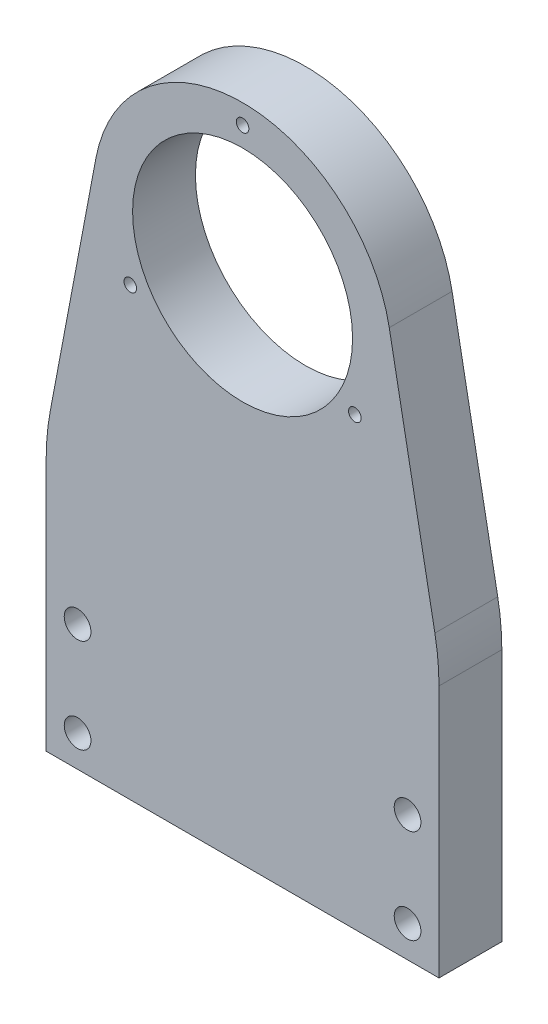
SolidWorks part; units mm, degrees
ref_plane "정면" through (0, 0, 0) normal (0, 0, 1) x (1, 0, 0)
ref_plane "윗면" through (0, 0, 0) normal (0, 1, 0) x (1, 0, 0)
ref_plane "우측면" through (0, 0, 0) normal (1, 0, 0) x (0, 0, -1)
sketch "스케치1" plane through (0, 0, 0) normal (0, 0, 1) x (1, 0, 0)
  line L0 (0, 0) -> (50, 0)
  line L1 (50, 0) -> (50, 35)
  line L2 (50, 35) -> (43.6701, 68.5251)
  line L3 (25, 0) -> (25, 65) construction
  line L4 (0, 35) -> (6.3299, 68.5251)
  line L5 (0, 0) -> (0, 35)
  circle A0 centre (25, 65) radius 19
  dimension "D1" = 38
  dimension "D3" = 65
  dimension "D4" = 50
  dimension "D5" = 35
extrude "보스-돌출1" add sketch "스케치1" along normal blind 8
fillet "필렛1" radius 30 2 edges at (0, 35, 4) (50, 35, 4)
sketch "스케치2" plane through (0, 0, 0) normal (0, 0, -1) x (-1, 0, 0)
  arc A0 (-6.3299, 68.5251) -> (-43.6701, 68.5251) centre (-25, 65) ccw construction
  arc A1 (-6.3299, 68.5251) -> (-43.6701, 68.5251) centre (-25, 65) ccw
  circle A2 centre (-25, 65) radius 14
  dimension "D1" = 28
extrude "컷-돌출1" cut sketch "스케치2" against normal up to next contours A2
hole_wizard "M3 육각 소켓 접시 머리 캡 나사용 카운터싱크1" positions "스케치3" profile "스케치4" countersink size "M3" standard "ISO" end condition up to next
sketch "스케치3" plane through (0, 0, 0) normal (0, 0, -1) x (-1, 0, 0)
  line L0 (-4, 16) -> (-4, 4)
  line L3 (0, 0) -> (0, 32.1927) construction
  line L4 (0, 0) -> (-50, 0) construction
  line L5 (-46, 16) -> (-46, 4)
  line L6 (-50, 0) -> (-50, 32.1927) construction
  point P0 (-4, 16)
  point P2 (-4, 4)
  point P20 (-46, 16)
  point P21 (-46, 4)
  point P30 (-46, 10)
  dimension "D1" = 12
  dimension "D2" = 4
  dimension "D3" = 4
  dimension "D4" = 4
sketch "스케치4" plane through (4, 16, 0) normal (1, 0, 0) x (0, 1, 0)
  line L0 (0, 0) -> (0, 8)
  line L1 (0, 8) -> (1.7, 8)
  line L2 (1.7, 8) -> (1.7, 1.66)
  line L3 (1.7, 1.66) -> (3.36, 0)
  line L5 (3.36, 0) -> (0, 0)
  line L6 (-1.7, 1.66) -> (-3.36, 0) construction
  line L11 (0, -6.35) -> (0, 107.95) construction
  dimension "관통 구멍 지름" = 3.4
  dimension "관통 구멍 깊이" = 8
  dimension "표면 카운터싱크 지름" = 6.72
  dimension "표면 카운터싱크 각도" = 90
hole_wizard "M3 나사 구멍1" positions "스케치5" profile "스케치6" tap size "M3" standard "ISO"
sketch "스케치5" plane through (0, 0, 0) normal (0, -1, 0) x (-1, 0, 0)
  line L0 (-38, -4) -> (-12, -4)
  line L2 (0, 0) -> (-50, 0) construction
  line L3 (0, -8) -> (0, 0) construction
  point P0 (-38, -4)
  point P2 (-12, -4)
  point P9 (-25, -4)
  point P12 (-25, 0)
  point P15 (0, -4)
  dimension "D1" = 12
sketch "스케치6" plane through (38, 0, 4) normal (1, 0, 0) x (0, 0, -1)
  line L0 (0, 0) -> (0, 9.2511)
  line L1 (0, 9.2511) -> (1.25, 8.5)
  line L2 (1.25, 8.5) -> (1.25, 0)
  line L5 (1.25, 0) -> (0, 0)
  line L10 (0, 9.2511) -> (-1.25, 8.5) construction
  line L11 (0, -6.35) -> (0, 107.95) construction
  dimension "탭 드릴 지름" = 2.5
  dimension "탭 드릴 깊이" = 8.5
  dimension "드릴 각도" = 118
cosmetic thread "구멍 나사산1" parameters "D1"=6, "D2"=3
cosmetic thread "구멍 나사산2" parameters "D1"=6, "D2"=3
hole_wizard "M2 나사 구멍1" positions "스케치7" profile "스케치8" tap size "M2" standard "ISO" end condition through all
sketch "스케치7" plane through (0, 0, 0) normal (0, 0, -1) x (-1, 0, 0)
  line L1 (-25, 81.5) -> (-39.2894, 56.75)
  line L2 (-39.2894, 56.75) -> (-10.7106, 56.75)
  line L3 (-10.7106, 56.75) -> (-25, 81.5)
  line L4 (-25, 84) -> (-25, 79)
  circle A0 centre (-25, 65) radius 16.5
  circle A1 centre (-25, 65) radius 16.5 construction
  arc A2 (-6.3299, 68.5251) -> (-43.6701, 68.5251) centre (-25, 65) ccw construction
  circle A3 centre (-25, 65) radius 14 construction
  point P7 (-25, 81.5)
  point P8 (-39.2894, 56.75)
  point P9 (-10.7106, 56.75)
  point P32 (-25, 81.5)
sketch "스케치8" plane through (10.7106, 56.75, 0) normal (1, 0, 0) x (0, 1, 0)
  line L0 (0, 0) -> (0, 8)
  line L1 (0, 8) -> (0.8, 8)
  line L2 (0.8, 8) -> (0.8, 0)
  line L5 (0.8, 0) -> (0, 0)
  line L11 (0, -6.35) -> (0, 107.95) construction
  dimension "관통 탭 드릴 지름" = 1.6
  dimension "관통 탭 드릴 깊이" = 8
cosmetic thread "구멍 나사산3" parameters "D2"=2
cosmetic thread "구멍 나사산4" parameters "D2"=2
cosmetic thread "구멍 나사산5" parameters "D2"=2
